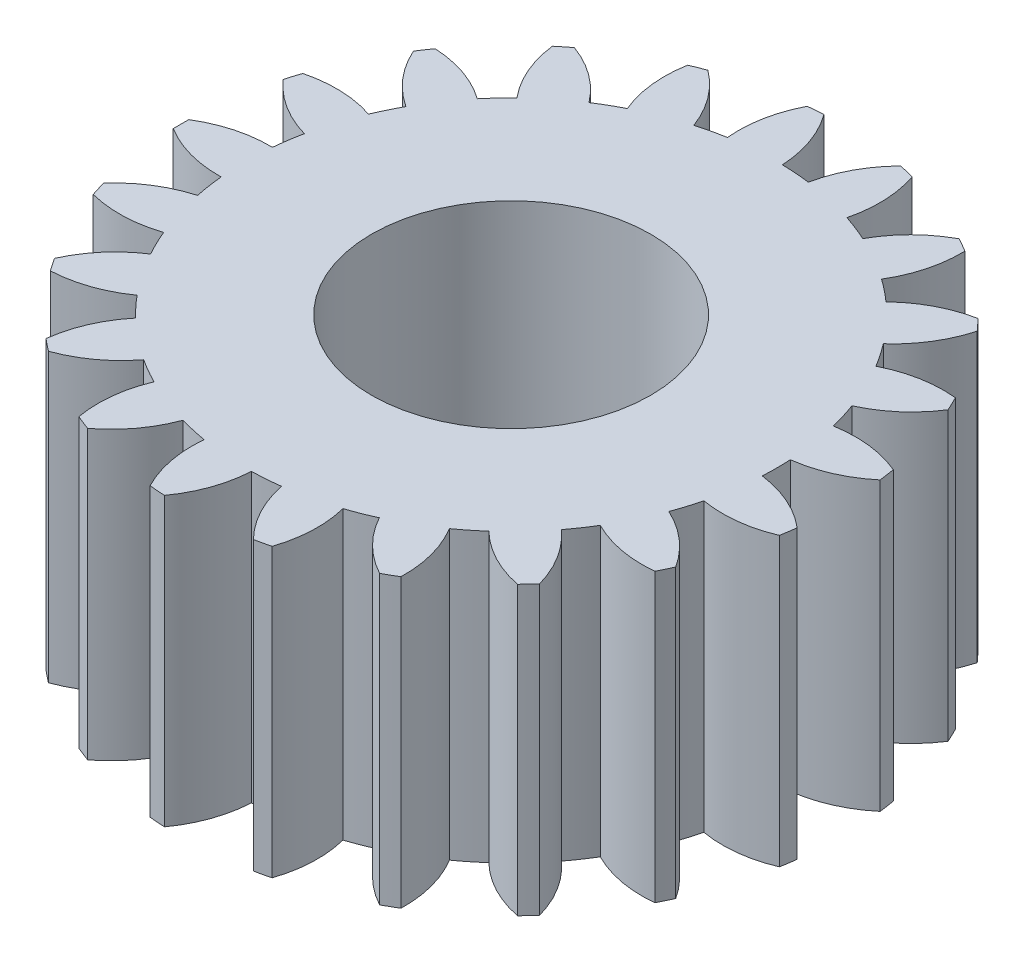
SolidWorks part; units mm, degrees
ref_plane "Front Plane" through (0, 0, 0) normal (0, 0, 1) x (1, 0, 0)
ref_plane "Top Plane" through (0, 0, 0) normal (0, 1, 0) x (1, 0, 0)
ref_plane "Right Plane" through (0, 0, 0) normal (1, 0, 0) x (0, 0, -1)
sketch "Sketch1" plane through (0, 0, 0) normal (0, 1, 0) x (1, 0, 0)
  circle A0 centre (0, 0) radius 27.5
  dimension "D1" = 55
extrude "Boss-Extrude1" add sketch "Sketch1" along normal blind 20
extrude "Cut-Extrude1" cut sketch "Sketch2" against normal blind 15
sketch "Sketch2" plane through (-17.5533, 15, -44.6937) normal (0, 1, 0) x (1, 0, 0)
  circle A0 centre (17.5533, -44.6937) radius 27.5
  arc A168 (19.9079, -63.0422) -> (22.1389, -67.2319) centre (28.1356, -61.3498) ccw
  arc A169 (22.1389, -67.2319) -> (23.2009, -66.9895) centre (17.5533, -44.6937) ccw
  arc A170 (23.2009, -66.9895) -> (23.3931, -62.2467) centre (15.2458, -64.2918) ccw
  arc A171 (23.3931, -62.2467) -> (25.2116, -61.533) centre (17.5533, -44.6937) ccw
  arc A172 (25.2116, -61.533) -> (28.5784, -64.879) centre (32.575, -57.4907) ccw
  arc A173 (28.5784, -64.879) -> (29.5218, -64.3343) centre (17.5533, -44.6937) ccw
  arc A174 (29.5218, -64.3343) -> (28.3075, -59.7456) centre (21.125, -64.1013) ccw
  arc A175 (28.3075, -59.7456) -> (29.8349, -58.5276) centre (17.5533, -44.6937) ccw
  arc A176 (29.8349, -58.5276) -> (34.0383, -60.7325) centre (35.6796, -52.4944) ccw
  arc A177 (34.0383, -60.7325) -> (34.7793, -59.934) centre (17.5533, -44.6937) ccw
  arc A178 (34.7793, -59.934) -> (32.2664, -55.907) centre (26.6868, -62.1863) ccw
  arc A179 (32.2664, -55.907) -> (33.3668, -54.2929) centre (17.5533, -44.6937) ccw
  arc A180 (33.3668, -54.2929) -> (38.0335, -55.1609) centre (37.1736, -46.805) ccw
  arc A181 (38.0335, -55.1609) -> (38.5061, -54.1795) centre (17.5533, -44.6937) ccw
  arc A182 (38.5061, -54.1795) -> (34.9179, -51.0721) centre (31.4371, -58.717) ccw
  arc A183 (34.9179, -51.0721) -> (35.4937, -49.2054) centre (17.5533, -44.6937) ccw
  arc A184 (35.4937, -49.2054) -> (40.2089, -48.6592) centre (36.9243, -40.9281) ccw
  arc A185 (40.2089, -48.6592) -> (40.3712, -47.5821) centre (17.5533, -44.6937) ccw
  arc A186 (40.3712, -47.5821) -> (36.0265, -45.6704) centre (34.9537, -54.0017) ccw
  arc A187 (36.0265, -45.6704) -> (36.0265, -43.7169) centre (17.5533, -44.6937) ccw
  arc A188 (36.0265, -43.7169) -> (40.3712, -41.8052) centre (34.9537, -35.3857) ccw
  arc A189 (40.3712, -41.8052) -> (40.2089, -40.7281) centre (17.5533, -44.6937) ccw
  arc A190 (40.2089, -40.7281) -> (35.4937, -40.182) centre (36.9243, -48.4593) ccw
  arc A191 (35.4937, -40.182) -> (34.9179, -38.3152) centre (17.5533, -44.6937) ccw
  arc A192 (34.9179, -38.3152) -> (38.5061, -35.2079) centre (31.4371, -30.6703) ccw
  arc A193 (38.5061, -35.2079) -> (38.0335, -34.2264) centre (17.5533, -44.6937) ccw
  arc A194 (38.0335, -34.2264) -> (33.3668, -35.0944) centre (37.1736, -42.5823) ccw
  arc A195 (33.3668, -35.0944) -> (32.2664, -33.4803) centre (17.5533, -44.6937) ccw
  arc A196 (32.2664, -33.4803) -> (34.7793, -29.4533) centre (26.6868, -27.201) ccw
  arc A197 (34.7793, -29.4533) -> (34.0383, -28.6548) centre (17.5533, -44.6937) ccw
  arc A198 (34.0383, -28.6548) -> (29.8349, -30.8598) centre (35.6796, -36.8929) ccw
  arc A199 (29.8349, -30.8598) -> (28.3075, -29.6417) centre (17.5533, -44.6937) ccw
  arc A200 (28.3075, -29.6417) -> (29.5218, -25.053) centre (21.125, -25.286) ccw
  arc A201 (29.5218, -25.053) -> (28.5784, -24.5083) centre (17.5533, -44.6937) ccw
  arc A202 (28.5784, -24.5083) -> (25.2116, -27.8543) centre (32.575, -31.8967) ccw
  arc A203 (25.2116, -27.8543) -> (23.3931, -27.1406) centre (17.5533, -44.6937) ccw
  arc A204 (23.3931, -27.1406) -> (23.2009, -22.3978) centre (15.2458, -25.0955) ccw
  arc A205 (23.2009, -22.3978) -> (22.1389, -22.1554) centre (17.5533, -44.6937) ccw
  arc A206 (22.1389, -22.1554) -> (19.9079, -26.3451) centre (28.1356, -28.0375) ccw
  arc A207 (19.9079, -26.3451) -> (17.9598, -26.1991) centre (17.5533, -44.6937) ccw
  arc A208 (17.9598, -26.1991) -> (16.3782, -21.7237) centre (9.5717, -26.6463) ccw
  arc A209 (16.3782, -21.7237) -> (15.2919, -21.8051) centre (17.5533, -44.6937) ccw
  arc A210 (15.2919, -21.8051) -> (14.395, -26.4663) centre (22.756, -25.6583) ccw
  arc A211 (14.395, -26.4663) -> (12.4904, -26.901) centre (17.5533, -44.6937) ccw
  arc A212 (12.4904, -26.901) -> (9.6599, -23.0906) centre (4.6068, -29.8007) ccw
  arc A213 (9.6599, -23.0906) -> (8.6458, -23.4886) centre (17.5533, -44.6937) ccw
  arc A214 (8.6458, -23.4886) -> (9.1627, -28.207) centre (16.9141, -24.9705) ccw
  arc A215 (9.1627, -28.207) -> (7.4708, -29.1838) centre (17.5533, -44.6937) ccw
  arc A216 (7.4708, -29.1838) -> (3.6429, -26.377) centre (0.7922, -34.2785) ccw
  arc A217 (3.6429, -26.377) -> (2.7913, -27.0562) centre (17.5533, -44.6937) ccw
  arc A218 (2.7913, -27.0562) -> (4.6759, -31.4127) centre (11.129, -26.0351) ccw
  arc A219 (4.6759, -31.4127) -> (3.3471, -32.8447) centre (17.5533, -44.6937) ccw
  arc A220 (3.3471, -32.8447) -> (-1.138, -31.2909) centre (-1.5331, -39.6816) ccw
  arc A221 (-1.138, -31.2909) -> (-1.7516, -32.191) centre (17.5533, -44.6937) ccw
  arc A222 (-1.7516, -32.191) -> (1.3334, -35.7984) centre (5.9147, -28.7577) ccw
  arc A223 (1.3334, -35.7984) -> (0.4858, -37.5585) centre (17.5533, -44.6937) ccw
  arc A224 (0.4858, -37.5585) -> (-4.2581, -37.3957) centre (-2.1625, -45.5301) ccw
  arc A225 (-4.2581, -37.3957) -> (-4.5792, -38.4367) centre (17.5533, -44.6937) ccw
  arc A226 (-4.5792, -38.4367) -> (-0.5679, -40.9745) centre (1.7346, -32.8962) ccw
  arc A227 (-0.5679, -40.9745) -> (-0.8591, -42.9062) centre (17.5533, -44.6937) ccw
  arc A228 (-0.8591, -42.9062) -> (-5.4402, -44.149) centre (-1.04, -51.3043) ccw
  arc A229 (-5.4402, -44.149) -> (-5.4402, -45.2383) centre (17.5533, -44.6937) ccw
  arc A230 (-5.4402, -45.2383) -> (-0.8591, -46.4811) centre (-1.04, -38.083) ccw
  arc A231 (-0.8591, -46.4811) -> (-0.5679, -48.4128) centre (17.5533, -44.6937) ccw
  arc A232 (-0.5679, -48.4128) -> (-4.5792, -50.9507) centre (1.7346, -56.4911) ccw
  arc A233 (-4.5792, -50.9507) -> (-4.2581, -51.9916) centre (17.5533, -44.6937) ccw
  arc A234 (-4.2581, -51.9916) -> (0.4858, -51.8288) centre (-2.1625, -43.8572) ccw
  arc A235 (0.4858, -51.8288) -> (1.3334, -53.5889) centre (17.5533, -44.6937) ccw
  arc A236 (1.3334, -53.5889) -> (-1.7516, -57.1964) centre (5.9147, -60.6296) ccw
  arc A237 (-1.7516, -57.1964) -> (-1.138, -58.0964) centre (17.5533, -44.6937) ccw
  arc A238 (-1.138, -58.0964) -> (3.3471, -56.5426) centre (-1.5331, -49.7057) ccw
  arc A239 (3.3471, -56.5426) -> (4.6759, -57.9747) centre (17.5533, -44.6937) ccw
  arc A240 (4.6759, -57.9747) -> (2.7913, -62.3312) centre (11.129, -63.3522) ccw
  arc A241 (2.7913, -62.3312) -> (3.6429, -63.0103) centre (17.5533, -44.6937) ccw
  arc A242 (3.6429, -63.0103) -> (7.4708, -60.2035) centre (0.7922, -55.1089) ccw
  arc A243 (7.4708, -60.2035) -> (9.1627, -61.1803) centre (17.5533, -44.6937) ccw
  arc A244 (9.1627, -61.1803) -> (8.6458, -65.8988) centre (16.9141, -64.4169) ccw
  arc A245 (8.6458, -65.8988) -> (9.6599, -66.2967) centre (17.5533, -44.6937) ccw
  arc A246 (9.6599, -66.2967) -> (12.4904, -62.4863) centre (4.6068, -59.5866) ccw
  arc A247 (12.4904, -62.4863) -> (14.395, -62.9211) centre (17.5533, -44.6937) ccw
  arc A248 (14.395, -62.9211) -> (15.2919, -67.5822) centre (22.756, -63.729) ccw
  arc A249 (15.2919, -67.5822) -> (16.3782, -67.6636) centre (17.5533, -44.6937) ccw
  arc A250 (16.3782, -67.6636) -> (17.9598, -63.1882) centre (9.5717, -62.741) ccw
  arc A251 (17.9598, -63.1882) -> (19.9079, -63.0422) centre (17.5533, -44.6937) ccw
sketch "Sketch5" plane through (0, 15, 0) normal (0, -1, 0) x (1, 0, 0)
  circle A1 centre (0, 0) radius 27.5
  circle A2 centre (0, 0) radius 27.5
  arc A84 (2.3546, 18.3485) -> (0.4065, 18.4945) centre (0, 0) ccw
  arc A85 (0.4065, 18.4945) -> (-1.1752, 22.97) centre (-7.9816, 18.0473) ccw
  arc A86 (-1.1752, 22.97) -> (-2.2614, 22.8886) centre (0, 0) ccw
  arc A87 (-2.2614, 22.8886) -> (-3.1584, 18.2274) centre (5.2027, 19.0354) ccw
  arc A88 (-3.1584, 18.2274) -> (-5.063, 17.7927) centre (0, 0) ccw
  arc A89 (-5.063, 17.7927) -> (-7.8935, 21.6031) centre (-12.9466, 14.8929) ccw
  arc A90 (-7.8935, 21.6031) -> (-8.9075, 21.2051) centre (0, 0) ccw
  arc A91 (-8.9075, 21.2051) -> (-8.3907, 16.4866) centre (-0.6392, 19.7232) ccw
  arc A92 (-8.3907, 16.4866) -> (-10.0825, 15.5099) centre (0, 0) ccw
  arc A93 (-10.0825, 15.5099) -> (-13.9104, 18.3167) centre (-16.7612, 10.4152) ccw
  arc A94 (-13.9104, 18.3167) -> (-14.7621, 17.6375) centre (0, 0) ccw
  arc A95 (-14.7621, 17.6375) -> (-12.8774, 13.281) centre (-6.4244, 18.6585) ccw
  arc A96 (-12.8774, 13.281) -> (-14.2062, 11.8489) centre (0, 0) ccw
  arc A97 (-14.2062, 11.8489) -> (-18.6913, 13.4027) centre (-19.0864, 5.012) ccw
  arc A98 (-18.6913, 13.4027) -> (-19.305, 12.5027) centre (0, 0) ccw
  arc A99 (-19.305, 12.5027) -> (-16.22, 8.8953) centre (-11.6386, 15.936) ccw
  arc A100 (-16.22, 8.8953) -> (-17.0676, 7.1352) centre (0, 0) ccw
  arc A101 (-17.0676, 7.1352) -> (-21.8115, 7.2979) centre (-19.7158, -0.8365) ccw
  arc A102 (-21.8115, 7.2979) -> (-22.1326, 6.257) centre (0, 0) ccw
  arc A103 (-22.1326, 6.257) -> (-18.1213, 3.7192) centre (-15.8188, 11.7974) ccw
  arc A104 (-18.1213, 3.7192) -> (-18.4124, 1.7874) centre (0, 0) ccw
  arc A105 (-18.4124, 1.7874) -> (-22.9936, 0.5447) centre (-18.5933, -6.6106) ccw
  arc A106 (-22.9936, 0.5447) -> (-22.9936, -0.5447) centre (0, 0) ccw
  arc A107 (-22.9936, -0.5447) -> (-18.4124, -1.7874) centre (-18.5933, 6.6106) ccw
  arc A108 (-18.4124, -1.7874) -> (-18.1213, -3.7192) centre (0, 0) ccw
  arc A109 (-18.1213, -3.7192) -> (-22.1326, -6.257) centre (-15.8188, -11.7974) ccw
  arc A110 (-22.1326, -6.257) -> (-21.8115, -7.2979) centre (0, 0) ccw
  arc A111 (-21.8115, -7.2979) -> (-17.0676, -7.1352) centre (-19.7158, 0.8365) ccw
  arc A112 (-17.0676, -7.1352) -> (-16.22, -8.8953) centre (0, 0) ccw
  arc A113 (-16.22, -8.8953) -> (-19.305, -12.5027) centre (-11.6386, -15.936) ccw
  arc A114 (-19.305, -12.5027) -> (-18.6913, -13.4027) centre (0, 0) ccw
  arc A115 (-18.6913, -13.4027) -> (-14.2062, -11.8489) centre (-19.0864, -5.012) ccw
  arc A116 (-14.2062, -11.8489) -> (-12.8774, -13.281) centre (0, 0) ccw
  arc A117 (-12.8774, -13.281) -> (-14.7621, -17.6375) centre (-6.4244, -18.6585) ccw
  arc A118 (-14.7621, -17.6375) -> (-13.9104, -18.3167) centre (0, 0) ccw
  arc A119 (-13.9104, -18.3167) -> (-10.0825, -15.5099) centre (-16.7612, -10.4152) ccw
  arc A120 (-10.0825, -15.5099) -> (-8.3907, -16.4866) centre (0, 0) ccw
  arc A121 (-8.3907, -16.4866) -> (-8.9075, -21.2051) centre (-0.6392, -19.7232) ccw
  arc A122 (-8.9075, -21.2051) -> (-7.8935, -21.6031) centre (0, 0) ccw
  arc A123 (-7.8935, -21.6031) -> (-5.063, -17.7927) centre (-12.9466, -14.8929) ccw
  arc A124 (-5.063, -17.7927) -> (-3.1584, -18.2274) centre (0, 0) ccw
  arc A125 (-3.1584, -18.2274) -> (-2.2614, -22.8886) centre (5.2027, -19.0354) ccw
  arc A126 (-2.2614, -22.8886) -> (-1.1752, -22.97) centre (0, 0) ccw
  arc A127 (-1.1752, -22.97) -> (0.4065, -18.4945) centre (-7.9816, -18.0473) ccw
  arc A128 (0.4065, -18.4945) -> (2.3546, -18.3485) centre (0, 0) ccw
  arc A129 (2.3546, -18.3485) -> (4.5855, -22.5383) centre (10.5823, -16.6562) ccw
  arc A130 (4.5855, -22.5383) -> (5.6475, -22.2959) centre (0, 0) ccw
  arc A131 (5.6475, -22.2959) -> (5.8398, -17.5531) centre (-2.3075, -19.5982) ccw
  arc A132 (5.8398, -17.5531) -> (7.6583, -16.8394) centre (0, 0) ccw
  arc A133 (7.6583, -16.8394) -> (11.0251, -20.1853) centre (15.0216, -12.797) ccw
  arc A134 (11.0251, -20.1853) -> (11.9685, -19.6407) centre (0, 0) ccw
  arc A135 (11.9685, -19.6407) -> (10.7542, -15.0519) centre (3.5717, -19.4076) ccw
  arc A136 (10.7542, -15.0519) -> (12.2815, -13.8339) centre (0, 0) ccw
  arc A137 (12.2815, -13.8339) -> (16.485, -16.0388) centre (18.1263, -7.8007) ccw
  arc A138 (16.485, -16.0388) -> (17.2259, -15.2403) centre (0, 0) ccw
  arc A139 (17.2259, -15.2403) -> (14.713, -11.2134) centre (9.1335, -17.4926) ccw
  arc A140 (14.713, -11.2134) -> (15.8135, -9.5993) centre (0, 0) ccw
  arc A141 (15.8135, -9.5993) -> (20.4802, -10.4672) centre (19.6203, -2.1114) ccw
  arc A142 (20.4802, -10.4672) -> (20.9528, -9.4858) centre (0, 0) ccw
  arc A143 (20.9528, -9.4858) -> (17.3646, -6.3785) centre (13.8838, -14.0233) ccw
  arc A144 (17.3646, -6.3785) -> (17.9404, -4.5117) centre (0, 0) ccw
  arc A145 (17.9404, -4.5117) -> (22.6556, -3.9656) centre (19.3709, 3.7656) ccw
  arc A146 (22.6556, -3.9656) -> (22.8179, -2.8884) centre (0, 0) ccw
  arc A147 (22.8179, -2.8884) -> (18.4732, -0.9768) centre (17.4004, -9.308) ccw
  arc A148 (18.4732, -0.9768) -> (18.4732, 0.9768) centre (0, 0) ccw
  arc A149 (18.4732, 0.9768) -> (22.8179, 2.8884) centre (17.4004, 9.308) ccw
  arc A150 (22.8179, 2.8884) -> (22.6556, 3.9656) centre (0, 0) ccw
  arc A151 (22.6556, 3.9656) -> (17.9404, 4.5117) centre (19.3709, -3.7656) ccw
  arc A152 (17.9404, 4.5117) -> (17.3646, 6.3785) centre (0, 0) ccw
  arc A153 (17.3646, 6.3785) -> (20.9528, 9.4858) centre (13.8838, 14.0233) ccw
  arc A154 (20.9528, 9.4858) -> (20.4802, 10.4672) centre (0, 0) ccw
  arc A155 (20.4802, 10.4672) -> (15.8135, 9.5993) centre (19.6203, 2.1114) ccw
  arc A156 (15.8135, 9.5993) -> (14.713, 11.2134) centre (0, 0) ccw
  arc A157 (14.713, 11.2134) -> (17.2259, 15.2403) centre (9.1335, 17.4926) ccw
  arc A158 (17.2259, 15.2403) -> (16.485, 16.0388) centre (0, 0) ccw
  arc A159 (16.485, 16.0388) -> (12.2815, 13.8339) centre (18.1263, 7.8007) ccw
  arc A160 (12.2815, 13.8339) -> (10.7542, 15.0519) centre (0, 0) ccw
  arc A161 (10.7542, 15.0519) -> (11.9685, 19.6407) centre (3.5717, 19.4076) ccw
  arc A162 (11.9685, 19.6407) -> (11.0251, 20.1853) centre (0, 0) ccw
  arc A163 (11.0251, 20.1853) -> (7.6583, 16.8394) centre (15.0216, 12.797) ccw
  arc A164 (7.6583, 16.8394) -> (5.8398, 17.5531) centre (0, 0) ccw
  arc A165 (5.8398, 17.5531) -> (5.6475, 22.2959) centre (-2.3075, 19.5982) ccw
  arc A166 (5.6475, 22.2959) -> (4.5855, 22.5383) centre (0, 0) ccw
  arc A167 (4.5855, 22.5383) -> (2.3546, 18.3485) centre (10.5823, 16.6562) ccw
  arc A168 (2.3546, 18.3485) -> (0.4065, 18.4945) centre (0, 0) ccw
  arc A169 (0.4065, 18.4945) -> (-1.1752, 22.97) centre (-7.9816, 18.0473) ccw
  arc A170 (-1.1752, 22.97) -> (-2.2614, 22.8886) centre (0, 0) ccw
  arc A171 (-2.2614, 22.8886) -> (-3.1584, 18.2274) centre (5.2027, 19.0354) ccw
  arc A172 (-3.1584, 18.2274) -> (-5.063, 17.7927) centre (0, 0) ccw
  arc A173 (-5.063, 17.7927) -> (-7.8935, 21.6031) centre (-12.9466, 14.8929) ccw
  arc A174 (-7.8935, 21.6031) -> (-8.9075, 21.2051) centre (0, 0) ccw
  arc A175 (-8.9075, 21.2051) -> (-8.3907, 16.4866) centre (-0.6392, 19.7232) ccw
  arc A176 (-8.3907, 16.4866) -> (-10.0825, 15.5099) centre (0, 0) ccw
  arc A177 (-10.0825, 15.5099) -> (-13.9104, 18.3167) centre (-16.7612, 10.4152) ccw
  arc A178 (-13.9104, 18.3167) -> (-14.7621, 17.6375) centre (0, 0) ccw
  arc A179 (-14.7621, 17.6375) -> (-12.8774, 13.281) centre (-6.4244, 18.6585) ccw
  arc A180 (-12.8774, 13.281) -> (-14.2062, 11.8489) centre (0, 0) ccw
  arc A181 (-14.2062, 11.8489) -> (-18.6913, 13.4027) centre (-19.0864, 5.012) ccw
  arc A182 (-18.6913, 13.4027) -> (-19.305, 12.5027) centre (0, 0) ccw
  arc A183 (-19.305, 12.5027) -> (-16.22, 8.8953) centre (-11.6386, 15.936) ccw
  arc A184 (-16.22, 8.8953) -> (-17.0676, 7.1352) centre (0, 0) ccw
  arc A185 (-17.0676, 7.1352) -> (-21.8115, 7.2979) centre (-19.7158, -0.8365) ccw
  arc A186 (-21.8115, 7.2979) -> (-22.1326, 6.257) centre (0, 0) ccw
  arc A187 (-22.1326, 6.257) -> (-18.1213, 3.7192) centre (-15.8188, 11.7974) ccw
  arc A188 (-18.1213, 3.7192) -> (-18.4124, 1.7874) centre (0, 0) ccw
  arc A189 (-18.4124, 1.7874) -> (-22.9936, 0.5447) centre (-18.5933, -6.6106) ccw
  arc A190 (-22.9936, 0.5447) -> (-22.9936, -0.5447) centre (0, 0) ccw
  arc A191 (-22.9936, -0.5447) -> (-18.4124, -1.7874) centre (-18.5933, 6.6106) ccw
  arc A192 (-18.4124, -1.7874) -> (-18.1213, -3.7192) centre (0, 0) ccw
  arc A193 (-18.1213, -3.7192) -> (-22.1326, -6.257) centre (-15.8188, -11.7974) ccw
  arc A194 (-22.1326, -6.257) -> (-21.8115, -7.2979) centre (0, 0) ccw
  arc A195 (-21.8115, -7.2979) -> (-17.0676, -7.1352) centre (-19.7158, 0.8365) ccw
  arc A196 (-17.0676, -7.1352) -> (-16.22, -8.8953) centre (0, 0) ccw
  arc A197 (-16.22, -8.8953) -> (-19.305, -12.5027) centre (-11.6386, -15.936) ccw
  arc A198 (-19.305, -12.5027) -> (-18.6913, -13.4027) centre (0, 0) ccw
  arc A199 (-18.6913, -13.4027) -> (-14.2062, -11.8489) centre (-19.0864, -5.012) ccw
  arc A200 (-14.2062, -11.8489) -> (-12.8774, -13.281) centre (0, 0) ccw
  arc A201 (-12.8774, -13.281) -> (-14.7621, -17.6375) centre (-6.4244, -18.6585) ccw
  arc A202 (-14.7621, -17.6375) -> (-13.9104, -18.3167) centre (0, 0) ccw
  arc A203 (-13.9104, -18.3167) -> (-10.0825, -15.5099) centre (-16.7612, -10.4152) ccw
  arc A204 (-10.0825, -15.5099) -> (-8.3907, -16.4866) centre (0, 0) ccw
  arc A205 (-8.3907, -16.4866) -> (-8.9075, -21.2051) centre (-0.6392, -19.7232) ccw
  arc A206 (-8.9075, -21.2051) -> (-7.8935, -21.6031) centre (0, 0) ccw
  arc A207 (-7.8935, -21.6031) -> (-5.063, -17.7927) centre (-12.9466, -14.8929) ccw
  arc A208 (-5.063, -17.7927) -> (-3.1584, -18.2274) centre (0, 0) ccw
  arc A209 (-3.1584, -18.2274) -> (-2.2614, -22.8886) centre (5.2027, -19.0354) ccw
  arc A210 (-2.2614, -22.8886) -> (-1.1752, -22.97) centre (0, 0) ccw
  arc A211 (-1.1752, -22.97) -> (0.4065, -18.4945) centre (-7.9816, -18.0473) ccw
  arc A212 (0.4065, -18.4945) -> (2.3546, -18.3485) centre (0, 0) ccw
  arc A213 (2.3546, -18.3485) -> (4.5855, -22.5383) centre (10.5823, -16.6562) ccw
  arc A214 (4.5855, -22.5383) -> (5.6475, -22.2959) centre (0, 0) ccw
  arc A215 (5.6475, -22.2959) -> (5.8398, -17.5531) centre (-2.3075, -19.5982) ccw
  arc A216 (5.8398, -17.5531) -> (7.6583, -16.8394) centre (0, 0) ccw
  arc A217 (7.6583, -16.8394) -> (11.0251, -20.1853) centre (15.0216, -12.797) ccw
  arc A218 (11.0251, -20.1853) -> (11.9685, -19.6407) centre (0, 0) ccw
  arc A219 (11.9685, -19.6407) -> (10.7542, -15.0519) centre (3.5717, -19.4076) ccw
  arc A220 (10.7542, -15.0519) -> (12.2815, -13.8339) centre (0, 0) ccw
  arc A221 (12.2815, -13.8339) -> (16.485, -16.0388) centre (18.1263, -7.8007) ccw
  arc A222 (16.485, -16.0388) -> (17.2259, -15.2403) centre (0, 0) ccw
  arc A223 (17.2259, -15.2403) -> (14.713, -11.2134) centre (9.1335, -17.4926) ccw
  arc A224 (14.713, -11.2134) -> (15.8135, -9.5993) centre (0, 0) ccw
  arc A225 (15.8135, -9.5993) -> (20.4802, -10.4672) centre (19.6203, -2.1114) ccw
  arc A226 (20.4802, -10.4672) -> (20.9528, -9.4858) centre (0, 0) ccw
  arc A227 (20.9528, -9.4858) -> (17.3646, -6.3785) centre (13.8838, -14.0233) ccw
  arc A228 (17.3646, -6.3785) -> (17.9404, -4.5117) centre (0, 0) ccw
  arc A229 (17.9404, -4.5117) -> (22.6556, -3.9656) centre (19.3709, 3.7656) ccw
  arc A230 (22.6556, -3.9656) -> (22.8179, -2.8884) centre (0, 0) ccw
  arc A231 (22.8179, -2.8884) -> (18.4732, -0.9768) centre (17.4004, -9.308) ccw
  arc A232 (18.4732, -0.9768) -> (18.4732, 0.9768) centre (0, 0) ccw
  arc A233 (18.4732, 0.9768) -> (22.8179, 2.8884) centre (17.4004, 9.308) ccw
  arc A234 (22.8179, 2.8884) -> (22.6556, 3.9656) centre (0, 0) ccw
  arc A235 (22.6556, 3.9656) -> (17.9404, 4.5117) centre (19.3709, -3.7656) ccw
  arc A236 (17.9404, 4.5117) -> (17.3646, 6.3785) centre (0, 0) ccw
  arc A237 (17.3646, 6.3785) -> (20.9528, 9.4858) centre (13.8838, 14.0233) ccw
  arc A238 (20.9528, 9.4858) -> (20.4802, 10.4672) centre (0, 0) ccw
  arc A239 (20.4802, 10.4672) -> (15.8135, 9.5993) centre (19.6203, 2.1114) ccw
  arc A240 (15.8135, 9.5993) -> (14.713, 11.2134) centre (0, 0) ccw
  arc A241 (14.713, 11.2134) -> (17.2259, 15.2403) centre (9.1335, 17.4926) ccw
  arc A242 (17.2259, 15.2403) -> (16.485, 16.0388) centre (0, 0) ccw
  arc A243 (16.485, 16.0388) -> (12.2815, 13.8339) centre (18.1263, 7.8007) ccw
  arc A244 (12.2815, 13.8339) -> (10.7542, 15.0519) centre (0, 0) ccw
  arc A245 (10.7542, 15.0519) -> (11.9685, 19.6407) centre (3.5717, 19.4076) ccw
  arc A246 (11.9685, 19.6407) -> (11.0251, 20.1853) centre (0, 0) ccw
  arc A247 (11.0251, 20.1853) -> (7.6583, 16.8394) centre (15.0216, 12.797) ccw
  arc A248 (7.6583, 16.8394) -> (5.8398, 17.5531) centre (0, 0) ccw
  arc A249 (5.8398, 17.5531) -> (5.6475, 22.2959) centre (-2.3075, 19.5982) ccw
  arc A250 (5.6475, 22.2959) -> (4.5855, 22.5383) centre (0, 0) ccw
  arc A251 (4.5855, 22.5383) -> (2.3546, 18.3485) centre (10.5823, 16.6562) ccw
  dimension "D1" = 0
  dimension "D2" = 0
extrude "Cut-Extrude4" cut sketch "Sketch5" against normal up to surface (5 mm away) up to face at (0, 20, 27.5)
sketch "Sketch3" plane through (0, 20, 0) normal (0, 1, 0) x (1, 0, 0)
  circle A0 centre (0, 0) radius 9.725
  dimension "D1" = 19.45
extrude "Cut-Extrude2" cut sketch "Sketch3" against normal blind 18
sketch "Sketch4" plane through (0, 2, 0) normal (0, 1, 0) x (1, 0, 0)
  circle A0 centre (0, 0) radius 5.5
  dimension "D1" = 11
extrude "Cut-Extrude3" cut sketch "Sketch4" against normal up to surface (2 mm away) up to face at (0, 0, 0)
